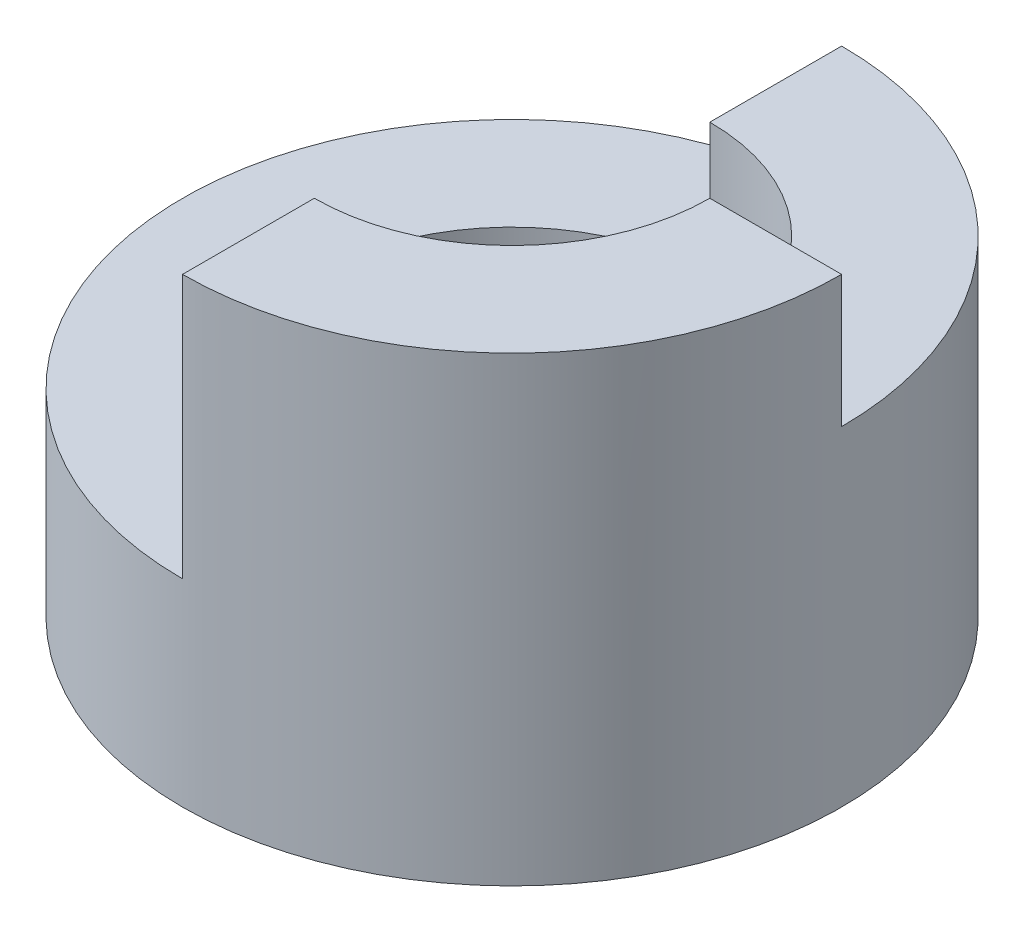
SolidWorks part; units mm, degrees
ref_plane "Front" through (0, 0, 0) normal (0, 0, 1) x (1, 0, 0)
ref_plane "Top" through (0, 0, 0) normal (0, 1, 0) x (1, 0, 0)
ref_plane "Right" through (0, 0, 0) normal (1, 0, 0) x (0, 0, -1)
sketch "Sketch1" plane through (0, 0, 0) normal (0, 1, 0) x (1, 0, 0)
  circle A0 centre (0, 0) radius 5
  circle A1 centre (0, 0) radius 3
  dimension "D1" = 6
  dimension "D2" = 10
extrude "Boss-Extrude1" add sketch "Sketch1" along normal blind 7
sketch "Sketch3" plane through (0, 7, 0) normal (0, 1, 0) x (1, 0, 0)
  line L1 (0, 5) -> (-6.2889, 5)
  line L2 (0, 5) -> (0, -5.4222)
  line L3 (0, -5.4222) -> (-6.2889, -5.4222)
  line L4 (-6.2889, 5) -> (-6.2889, -5.4222)
  circle A0 centre (0, 0) radius 5 construction
extrude "Cut-Extrude1" cut sketch "Sketch3" against normal blind 4
sketch "Sketch4" plane through (0, 7, 0) normal (0, 1, 0) x (1, 0, 0)
  line L1 (0, 5) -> (5, 5)
  line L2 (0, 5) -> (0, 0)
  line L3 (0, 0) -> (5, 0)
  line L4 (5, 5) -> (5, 0)
  arc A0 (0, -5) -> (0, 5) centre (0, 0) ccw construction
extrude "Cut-Extrude2" cut sketch "Sketch4" against normal blind 2
